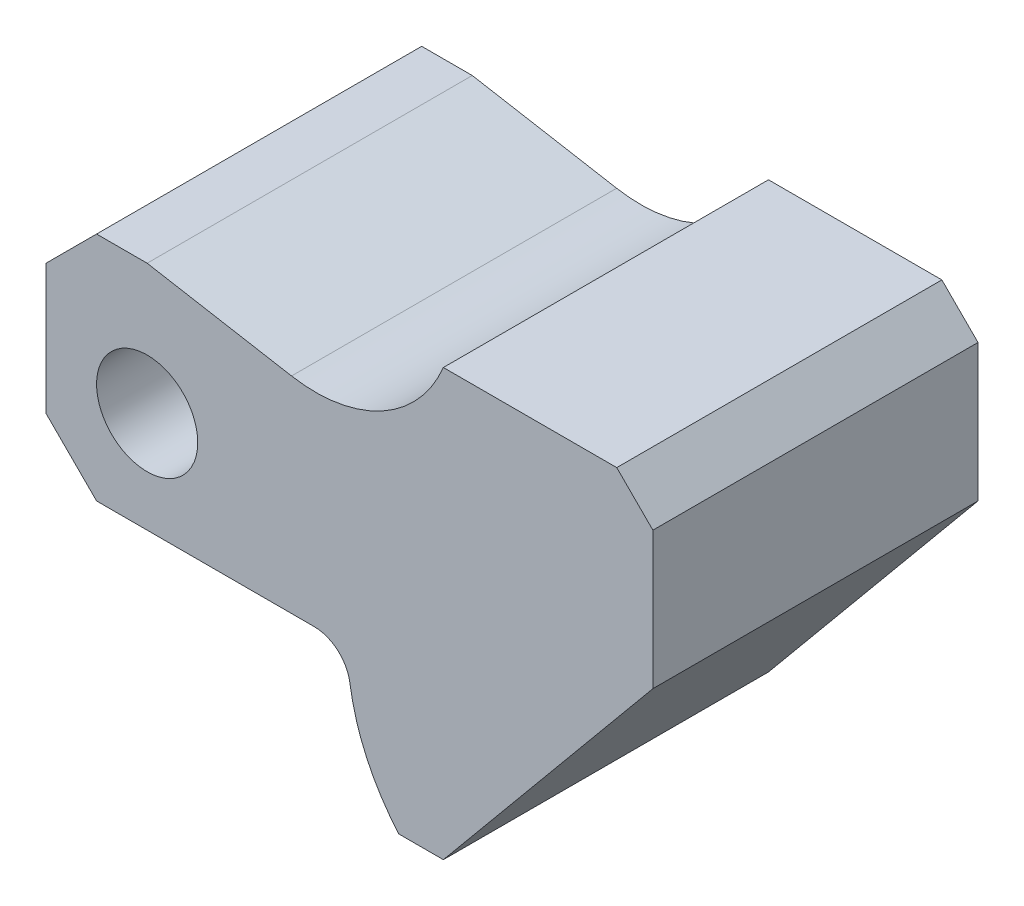
SolidWorks part; units mm, degrees
material "AISI 1020"
ref_plane "Plan de face" through (0, 0, 0) normal (0, 0, 1) x (1, 0, 0)
ref_plane "Plan de dessus" through (0, 0, 0) normal (0, 1, 0) x (1, 0, 0)
ref_plane "Plan de droite" through (0, 0, 0) normal (1, 0, 0) x (0, 0, -1)
sketch "Esquisse2" plane through (0, 0, 0) normal (0, 0, 1) x (1, 0, 0)
  line L0 (48.834, -19) -> (55, -19)
  line L1 (55, -19) -> (84, 16)
  line L2 (84, 16) -> (84, 35)
  line L3 (79, 40) -> (55, 40)
  line L4 (33.9849, 28.4761) -> (14, 32)
  line L5 (14, 32) -> (7, 32)
  line L6 (0, 25) -> (0, 7)
  line L7 (7, 0) -> (37.1125, 0)
  line L8 (7, 32) -> (0, 25)
  line L9 (0, 7) -> (7, 0)
  line L10 (84, 35) -> (79, 40)
  arc A0 (55, 40) -> (33.9849, 28.4761) centre (37.3103, 47.3354) cw
  arc A1 (37.1125, 0) -> (42.0582, -4.2647) centre (37.1125, -5) cw
  arc A2 (42.0582, -4.2647) -> (48.834, -19) centre (70.7429, 0) ccw
  circle A3 centre (14, 14) radius 7
  point P4 (84, 40)
  point P9 (0, 32)
  point P10 (0, 0)
  dimension "D3" = 29
  dimension "D7" = 19.1503
  dimension "D10" = 5
  dimension "D13" = 14
  dimension "A" = 84
  dimension "D2" = 59
  dimension "D4" = 29
  dimension "D5" = 24
  dimension "D6" = 14
  dimension "D8" = 10
  dimension "D9" = 32
  dimension "D11" = 14
  dimension "D12" = 14
  dimension "D14" = 19
  dimension "D15" = 29
  dimension "D16" = 19
  dimension "D17" = 7
  dimension "D18" = 45
  dimension "D19" = 7
  dimension "D20" = 45
  dimension "D21" = 5
  dimension "D22" = 45
extrude "Boss.-Extru.2" add sketch "Esquisse2" along normal mid plane 45
equation "\"A\" = 84"
equation "\"B\" = 59"
equation "\"C\"= 45"
